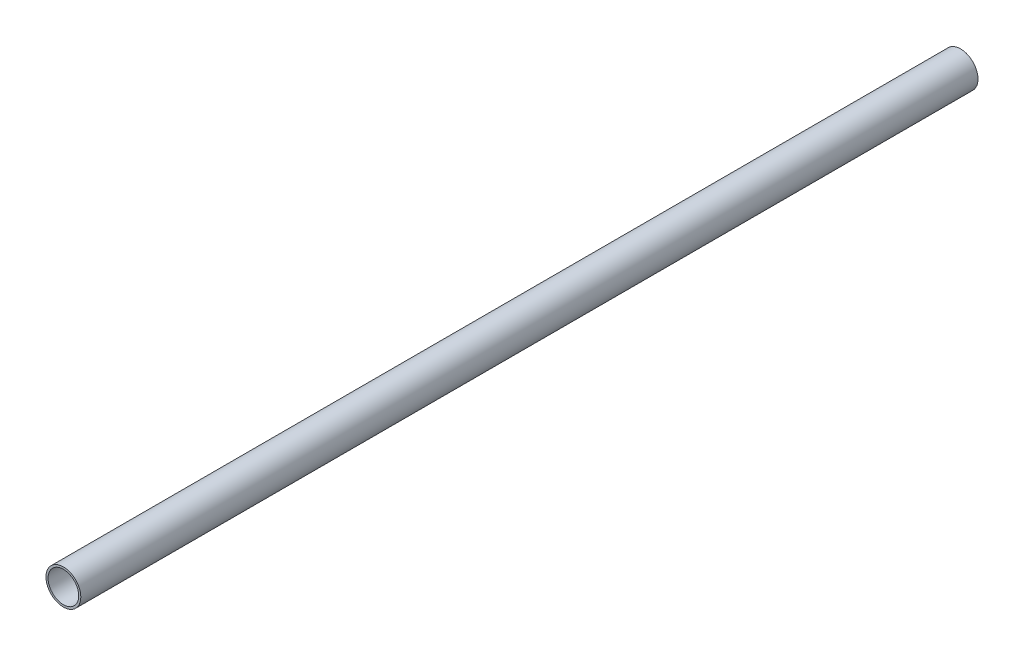
SolidWorks part; units mm, degrees
material "1.4301 (X5CrNi18-10)"
ref_plane "Plan de face" through (0, 0, 0) normal (0, 0, 1) x (1, 0, 0)
ref_plane "Plan de dessus" through (0, 0, 0) normal (0, 1, 0) x (1, 0, 0)
ref_plane "Plan de droite" through (0, 0, 0) normal (1, 0, 0) x (0, 0, -1)
sketch "Esquisse1" plane through (0, 0, 0) normal (0, 0, 1) x (1, 0, 0)
  circle A0 centre (0, 0) radius 11
  circle A1 centre (0, 0) radius 12.5
  dimension "D1" = 25
  dimension "D2" = 22
extrude "Boss.-Extru.1" add sketch "Esquisse1" along normal blind 644
